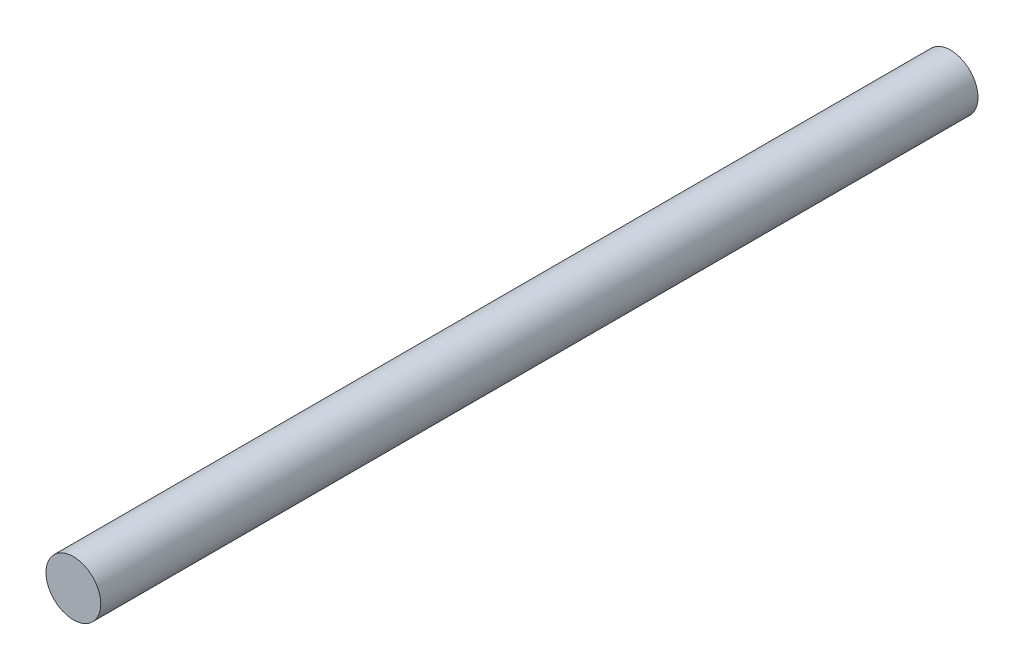
SolidWorks part; units mm, degrees
material "1.0036 (S235JRG1)"
ref_plane "Ön Düzlem" through (0, 0, 0) normal (0, 0, 1) x (1, 0, 0)
ref_plane "Üst Düzlem" through (0, 0, 0) normal (0, 1, 0) x (1, 0, 0)
ref_plane "Sağ Düzlem" through (0, 0, 0) normal (1, 0, 0) x (0, 0, -1)
sketch "Çizim1" plane through (0, 0, 0) normal (0, 0, 1) x (1, 0, 0)
  circle A0 centre (0, 0) radius 6
  dimension "D1" = 12
extrude "Yükseklik-Ekstrüzyon1" add sketch "Çizim1" along normal blind 192
